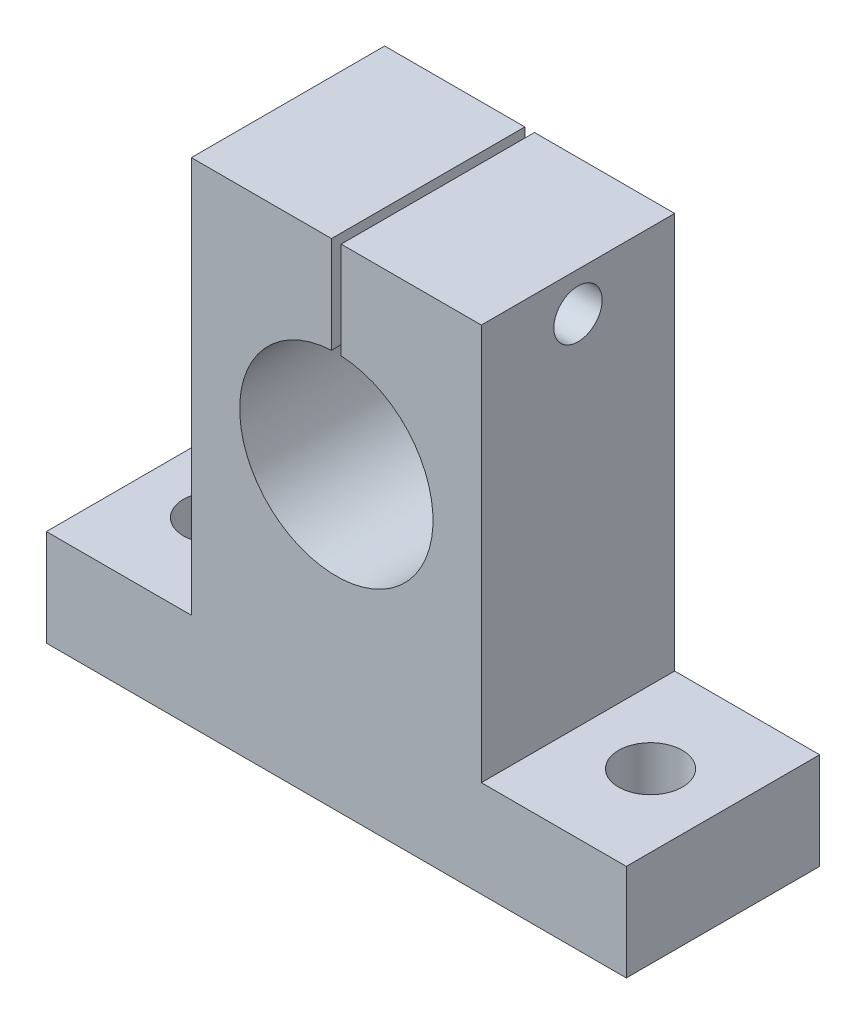
SolidWorks part; units mm, degrees
ref_plane "Front" through (0, 0, 0) normal (0, 0, 1) x (1, 0, 0)
ref_plane "Top" through (0, 0, 0) normal (0, 1, 0) x (1, 0, 0)
ref_plane "Right" through (0, 0, 0) normal (1, 0, 0) x (0, 0, -1)
sketch "Sketch1" plane through (0, 0, 0) normal (0, 0, 1) x (1, 0, 0)
  line L0 (0, 51) -> (0, -11.1975) construction
  line L1 (-30, 0) -> (30, 0)
  line L2 (-30, 0) -> (-30, 10)
  line L3 (-30, 10) -> (-15, 10)
  line L4 (30, 0) -> (30, 10)
  line L5 (15, 10) -> (30, 10)
  line L7 (-15, 10) -> (-15, 51)
  line L8 (-15, 51) -> (15, 51)
  line L9 (15, 10) -> (15, 51)
  circle A0 centre (0, 31) radius 10
  dimension "D4" = 20
  dimension "D1" = 10
  dimension "D2" = 60
  dimension "D3" = 30
  dimension "D5" = 51
  dimension "20" = 31
extrude "Boss-Extrude1" add sketch "Sketch1" along normal blind 20
sketch "Sketch2" plane through (15, 0, 0) normal (1, 0, 0) x (0, 0, -1)
  line L0 (-20, 51) -> (0, 51) construction
  line L1 (-10, 51) -> (-10, 14.0812) construction
  circle A0 centre (-10, 47) radius 2.5
  dimension "D1" = 5
  dimension "D2" = 4
sketch "Sketch3" plane through (0, 0, 20) normal (0, 0, 1) x (1, 0, 0)
  line L0 (15, 51) -> (-15, 51) construction
  line L1 (-0.5, 51) -> (0.5, 51)
  line L2 (-0.5, 51) -> (-0.5, 40.1491)
  line L3 (-0.5, 40.1491) -> (0.5, 40.1491)
  line L4 (0.5, 51) -> (0.5, 40.1491)
  line L5 (0, 51) -> (0, 12.111) construction
  dimension "D1" = 1
extrude "Cut-Extrude1" cut sketch "Sketch3" against normal blind 59 contours L4 L3 L2 L1
extrude "Cut-Extrude3" cut sketch "Sketch2" against normal blind 31 contours A0
sketch "Sketch5" plane through (0, 10, 0) normal (0, 1, 0) x (1, 0, 0)
  line L0 (0, 7.6779) -> (0, -23.3122) construction
  line L1 (30, -10) -> (-30, -10) construction
  line L4 (30, -20) -> (30, 0) construction
  line L5 (-30, -20) -> (-30, 0) construction
  circle A0 centre (22.5, -10) radius 3.3
  circle A1 centre (-22.5, -10) radius 3.3
  dimension "D1" = 45
  dimension "D2" = 6.6
extrude "Cut-Extrude5" cut sketch "Sketch5" against normal blind 22
